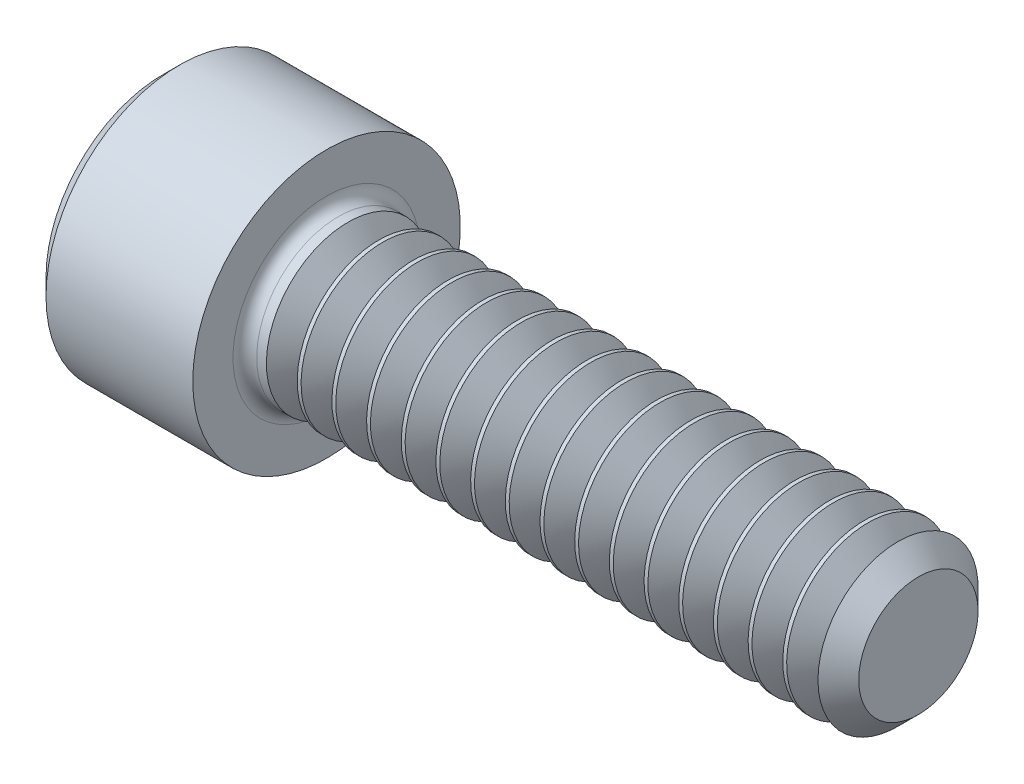
SolidWorks part; units mm, degrees
material "AISI Type 316L stainless steel"
ref_plane "Plane1" through (0, 0, 0) normal (0, 0, 1) x (1, 0, 0)
ref_plane "Plane2" through (0, 0, 0) normal (0, 1, 0) x (1, 0, 0)
ref_plane "Plane3" through (0, 0, 0) normal (1, 0, 0) x (0, 0, -1)
sketch "BodySke" plane through (0, 0, 0) normal (0, 0, 1) x (1, 0, 0)
  line L0 (0, 0) -> (0, 2.5146)
  line L1 (0.3556, 2.8702) -> (3.5052, 2.8702)
  line L2 (3.5052, 2.8702) -> (3.5052, 1.7526)
  line L3 (3.5052, 1.7526) -> (15.7328, 1.7526)
  line L4 (16.2052, 1.2802) -> (16.2052, 0)
  line L5 (16.2052, 0) -> (0, 0)
  line L6 (-31.75, 0) -> (127, 0) construction
  line L7 (0, 2.5146) -> (0.3556, 2.8702)
  line L8 (16.2052, 1.2802) -> (15.7328, 1.7526)
  line L9 (0, -2.5146) -> (0.3556, -2.8702) construction
  line L10 (16.2052, -1.2802) -> (15.7328, -1.7526) construction
  line L11 (4.2977, 9.525) -> (4.2977, 3.175) construction
  line L12 (3.5052, 9.525) -> (3.5052, 3.175) construction
  line L13 (-21.8948, 9.525) -> (-21.8948, 3.175) construction
  dimension "Diameter" = 3.5052
  dimension "Head_ht" = 3.5052
  dimension "Length" = 12.7
  dimension "Body_ch_ang" = 45
  dimension "Head_dia" = 5.7404
  dimension "Head_ch_ang" = 45
  dimension "Head_side_ht" = 3.1496
  dimension "Minor_dia" = 2.5603
  dimension "Advance" = 0.7925
  dimension "Thread_nom" = 12.7
  dimension "Thread_length" = 38.1
revolve "Base-Revolve" add sketch "BodySke"
cosmetic thread "ThreadCosmetic" [suppressed]
fillet "Fillet1" radius 0.254 1 edges at (3.5052, 0, 1.7526)
sketch "Sketch2" plane through (0, 0, 0) normal (0, 0, 1) x (1, 0, 0)
  line L0 (0, 1.3843) -> (1.6256, 1.3843)
  line L1 (1.6256, 1.3843) -> (2.4248, 0)
  line L2 (-31.75, 0) -> (127, 0) construction
  line L3 (2.4248, 0) -> (0, 0)
  line L4 (0, 0) -> (0, 1.3843)
  line L5 (0, 2.5146) -> (0, -2.5146) construction
  line L6 (0, 0) -> (47.625, 0) construction
  line L7 (3.5052, -2.8702) -> (3.5052, 2.8702) construction
  dimension "D1" = 1.3843
  dimension "D2" = 60
  dimension "Wall_thickness" = 1.8796
revolve "Hex-PreBroach" cut sketch "Sketch2" angle 360 about L6
sketch "Sketch3" plane through (0, 0, 0) normal (-1, 0, 0) x (0, 0.5, 0.866)
  line L0 (0.7992, 1.3843) -> (-0.7992, 1.3843)
  line L1 (-0.7992, 1.3843) -> (-1.5985, 0)
  line L2 (0.7992, 1.3843) -> (1.5985, 0)
  line L3 (0.7992, -1.3843) -> (1.5985, 0)
  line L4 (0.7992, -1.3843) -> (-0.7992, -1.3843)
  line L5 (-0.7992, -1.3843) -> (-1.5985, 0)
  dimension "D1" = 1.3843
  dimension "D2" = 1.3843
  dimension "Hex_size" = 2.7686
extrude "Hex" cut sketch "Sketch3" against normal blind 1.6256
sketch "Sketch4" plane through (0, 0, 0) normal (-1, 0, 0) x (0, 0, 1)
  line L0 (0, 0) -> (1.7399, 0)
  line L1 (0, 0) -> (6.1484, 3.5498) construction
  line L2 (0, 0) -> (0.8699, 1.5068)
  line L3 (1.4457, 0.3947) -> (1.6607, 0.5189)
  line L4 (1.0647, 1.0546) -> (1.2797, 1.1788)
  arc A0 (1.4457, 0.3947) -> (1.0647, 1.0546) centre (0, 0) ccw
  arc A1 (1.7399, 0) -> (1.6607, 0.5189) centre (0, 0) ccw
  arc A2 (0.8699, 1.5068) -> (1.2797, 1.1788) centre (0, 0) cw
  dimension "D1" = 30
  dimension "Spline_n_dim" = 2.9972
  dimension "Spline_m_dim" = 3.4798
  dimension "D2" = 60
  dimension "D3" = 0.381
  dimension "Spline_p_dim" = 0.762
extrude "Spline" [suppressed] cut sketch "Sketch4" against normal blind 1.6256
pattern_circular "CirPattern1" [suppressed] count 6 every 60
sketch "Sketch5" plane through (0, 0, 0) normal (0, 0, 1) x (1, 0, 0)
  line L0 (-31.75, 0) -> (127, 0) construction
  line L2 (0, 2.5146) -> (0, -2.5146) construction
  circle A0 centre (1.27, 0) radius 0.4445
  dimension "Drilled_hole_dia" = 0.889
  dimension "Drilled_hole_loc" = 1.27
extrude "Hole" [suppressed] cut sketch "Sketch5" against normal through all and the other way through all
pattern_circular "Drilled-4" [suppressed] count 2 every 60
pattern_circular "Drilled-6" [suppressed] count 3 every 60
sketch "ThdSchSke" plane through (0, 0, 0) normal (0, 0, 1) x (1, 0, 0)
  line L0 (4.2977, -1.2802) -> (3.9669, -1.7526)
  line L1 (4.2977, -1.2802) -> (4.6285, -1.7526)
  line L2 (4.6285, -1.7526) -> (4.6285, -2.1907)
  line L3 (-3.175, 0) -> (5.1513, 0) construction
  line L5 (4.6285, -2.1907) -> (3.9669, -2.1907)
  line L6 (3.9669, -2.1907) -> (3.9669, -1.7526)
  line L7 (0, 2.5146) -> (0, -2.5146) construction
  dimension "Thread_minor" = 2.5603
  dimension "Diameter" = 3.5052
  dimension "Start" = 4.2977
  dimension "SideAngle" = 55
  dimension "VeeAngle" = 70
  dimension "Overcut" = 4.3815
revolve "ThreadSchematic" cut sketch "ThdSchSke" angle 360 about L3
pattern_linear "ThdSchPat" count 16 spacing 0.7442 along (1, 0, 0) of "ThreadSchematic"
equation "\"D2@Sketch3\" = \"Hex_size@Sketch3\" / 2"
equation "\"D1@Sketch3\" = \"Hex_size@Sketch3\" / 2"
equation "\"D1@Sketch2\" = \"Hex_size@Sketch3\" / 2"
equation "\"D3@Sketch4\" = \"Spline_p_dim@Sketch4\" / 2"
equation "\"Thread_minor@ThreadCosmetic\"  =  \"Minor_dia@BodySke\""
equation "\"D2@CirPattern1\" = 360 / \"Num_teeth@CirPattern1\""
equation "\"Wall_thickness@Sketch2\" = \"Head_ht@BodySke\" - \"Key_eng@Hex\""
equation "\"Thread_length@ThreadCosmetic\" = ((sgn( (\"Length@BodySke\" - \"Advance@BodySke\" ) - \"Thread_nom@BodySke\" )-1)*( (\"Length@BodySke\" - \"Advance@BodySke\" ) - \"Thread_nom@BodySke\" ))/-2+ \"Thread_nom@BodySke\""
equation "\"Thread_minor@ThdSchSke\" = \"Minor_dia@BodySke\""
equation "\"Diameter@ThdSchSke\" = \"Diameter@BodySke\""
equation "\"Overcut@ThdSchSke\" = \"Diameter@BodySke\" * 1.25"
equation "\"Start@ThdSchSke\" = \"Head_ht@BodySke\" + \"Length@BodySke\" - \"Thread_length@ThreadCosmetic\"  '---Non-countersunk---"
equation "\"Num_threads@ThdSchPat\" = int( \"Thread_length@ThreadCosmetic\" / \"Advance@BodySke\" + 0.999 )  + 1"
equation "\"Advance@ThdSchPat\" = \"Thread_length@ThreadCosmetic\" /  (\"Num_threads@ThdSchPat\" - 1) 'relax it"
equation "\"Num_threads@ThdSchPat\" = \"Num_threads@ThdSchPat\" - sgn( \"Num_threads@ThdSchPat\" - 1) '---chamfered tips only---"
